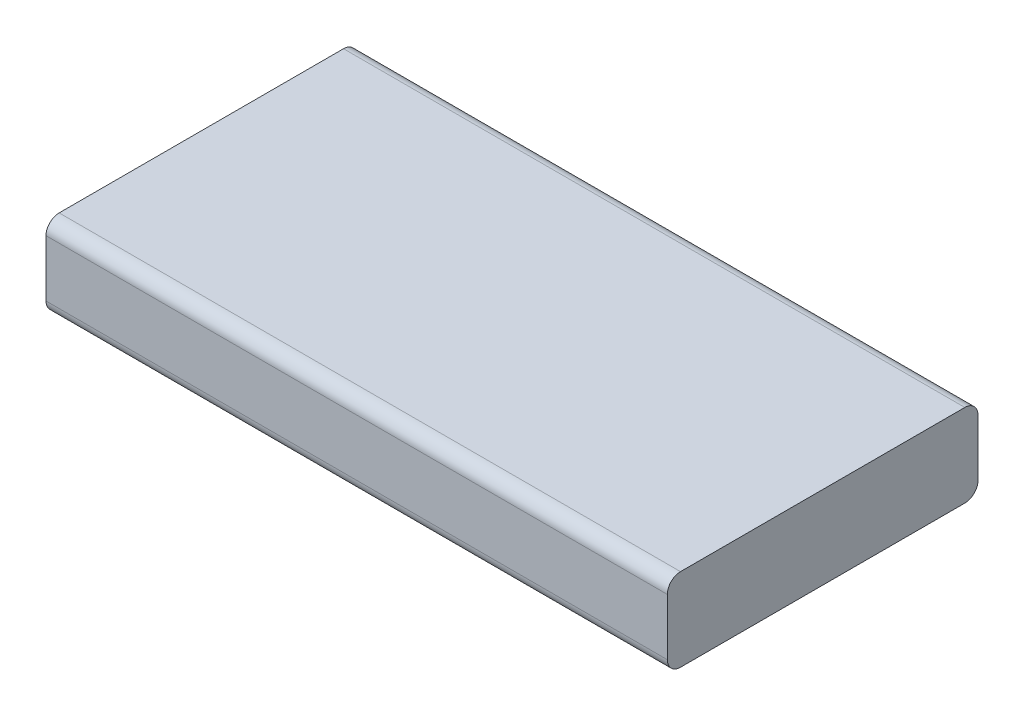
SolidWorks part; units mm, degrees
ref_plane "Front Plane" through (0, 0, 0) normal (0, 0, 1) x (1, 0, 0)
ref_plane "Top Plane" through (0, 0, 0) normal (0, 1, 0) x (1, 0, 0)
ref_plane "Right Plane" through (0, 0, 0) normal (1, 0, 0) x (0, 0, -1)
sketch "Sketch1" plane through (0, 0, 0) normal (0, 1, 0) x (1, 0, 0)
  line L1 (0, 0) -> (30, 0)
  line L2 (0, 0) -> (0, 15)
  line L3 (0, 15) -> (30, 15)
  line L4 (30, 0) -> (30, 15)
  dimension "D1" = 30
  dimension "D2" = 15
extrude "Boss-Extrude1" add sketch "Sketch1" along normal blind 4
fillet "Fillet1" radius 0.635 4 edges at (15, 0, -15) (15, 4, -15) (15, 0, 0) (15, 4, 0)
